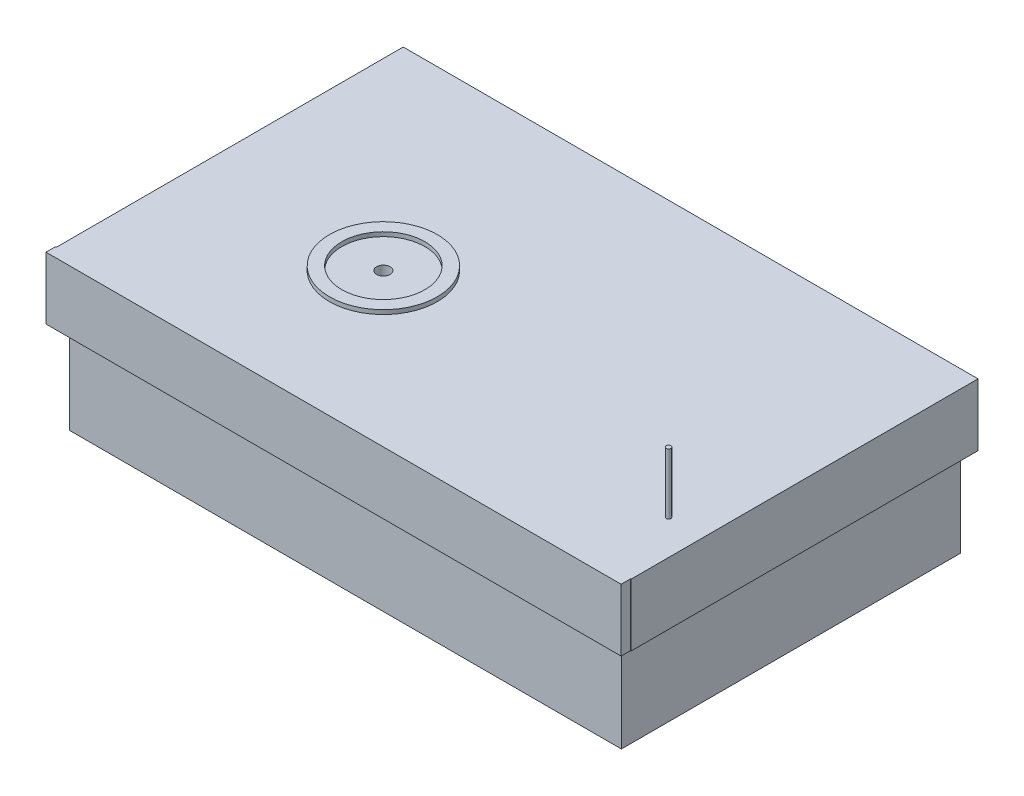
SolidWorks part; units mm, degrees
ref_plane "Alzado" through (0, 0, 0) normal (0, 0, 1) x (1, 0, 0)
ref_plane "Planta" through (0, 0, 0) normal (0, 1, 0) x (1, 0, 0)
ref_plane "Vista lateral" through (0, 0, 0) normal (1, 0, 0) x (0, 0, -1)
sketch "Croquis1" plane through (0, 0, 0) normal (0, 1, 0) x (1, 0, 0)
  line L0 (-102.8069, 0) -> (167.1931, 0)
  line L1 (-102.8069, 0) -> (-102.8069, 240)
  line L2 (-102.8069, 240) -> (167.1931, 240)
  line L3 (167.1931, 240) -> (167.1931, 0)
  line L4 (171.0384, 240) -> (171.0384, 0)
  line L5 (171.0384, 0) -> (287.5384, 0)
  line L6 (287.5384, 0) -> (287.5384, 240)
  line L7 (287.5384, 240) -> (171.0384, 240)
  dimension "D1" = 116.5
extrude "Saliente-Extruir1" add sketch "Croquis1" along normal blind 30
sketch "Croquis2" plane through (0, 0, 0) normal (0, 1, 0) x (1, 0, 0)
  line L0 (-102.8619, 0) -> (287.5384, 0)
  line L1 (287.5384, 0) -> (287.5384, 240)
  line L2 (-102.8619, 0) -> (-102.8069, 240)
  line L3 (-102.8069, 240) -> (287.5384, 240)
extrude "Saliente-Extruir3" add sketch "Croquis2" against normal blind 63.5
sketch "Croquis3" plane through (0, 0, 0) normal (0, 0, 1) x (1, 0, 0)
  line L0 (294.4077, 0) -> (-112.3522, 0)
  line L1 (-112.3522, 0) -> (-112.3522, 44.0543)
  line L2 (-112.3522, 44.0543) -> (294.4077, 44.0543)
  line L3 (294.4077, 44.0543) -> (294.4077, 0)
extrude "Saliente-Extruir4" add sketch "Croquis3" against normal blind 245.5
sketch "Croquis4" plane through (0, 44.0543, 0) normal (0, 1, 0) x (1, 0, 0)
  line L0 (-112.3522, 0) -> (17.6478, 0)
  line L1 (294.4077, 0) -> (-112.3522, 0) construction
  line L2 (-112.3522, 0) -> (-112.3522, 101.4505)
  line L4 (-112.3522, 245.5) -> (-112.3522, 0) construction
  circle A0 centre (17.6478, 101.4505) radius 38.1539
  circle A1 centre (17.6478, 101.4505) radius 29.4156
extrude "Saliente-Extruir5" add sketch "Croquis4" along normal blind 3 contours A0 A1
sketch "Croquis5" plane through (0, 0, 0) normal (0, 1, 0) x (1, 0, 0)
  circle A0 centre (17.6478, 101.4505) radius 4.7645
  dimension "D1" = 9.529
extrude "Cortar-Extruir1" cut sketch "Croquis5" along normal blind 142
sketch "Croquis6" plane through (0, 0, 0) normal (1, 0, 0) x (0, 0, -1)
  line L0 (0, 44.0543) -> (-6.6553, 44.0543)
  line L1 (-6.6553, 44.0543) -> (-6.6553, 0)
  line L2 (-6.6553, 0) -> (0, 0)
  line L3 (0, 44.0543) -> (0, 0)
extrude "Saliente-Extruir6" add sketch "Croquis6" along normal blind 294 and the other way blind 113
sketch "Croquis7" plane through (0, 0, 0) normal (0, 1, 0) x (1, 0, 0)
  circle A0 centre (269.7053, 51.2313) radius 1.651
  dimension "D1" = 3.302
extrude "Saliente-Extruir8" add sketch "Croquis7" along normal blind 112 and the other way blind 2
sketch "Croquis8" plane through (0, 0, 0) normal (0, 0, 1) x (1, 0, 0)
  line L0 (268.0543, 112) -> (271.3563, 112)
  line L1 (271.3563, 112) -> (271.3563, 87.0111)
  line L2 (271.3563, 44.0543) -> (271.3563, 112) construction
  line L3 (271.3563, 87.0111) -> (268.0543, 87.0111)
  line L4 (268.0543, 112) -> (268.0543, 44.0543) construction
  line L5 (268.0543, 87.0111) -> (268.0543, 112)
extrude "Cortar-Extruir2" cut sketch "Croquis8" against normal blind 112
